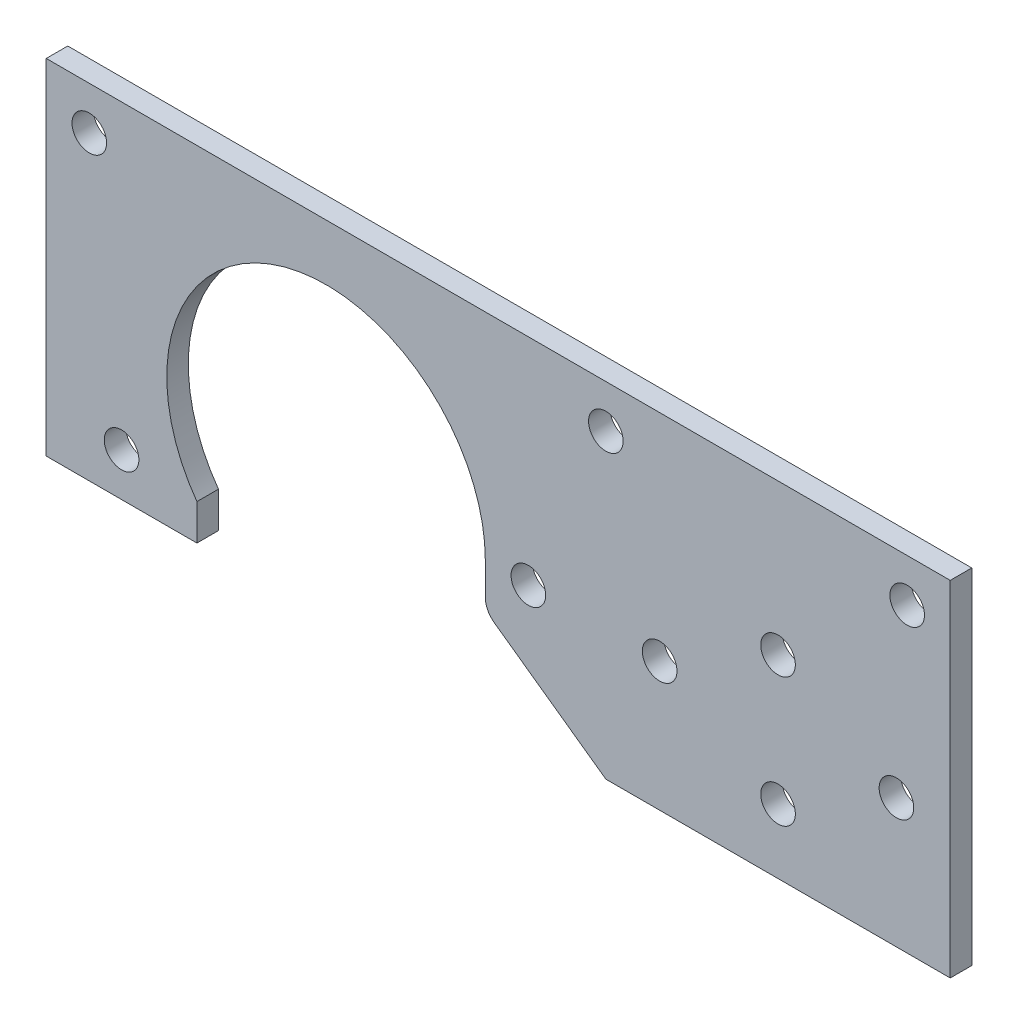
SolidWorks part; units mm, degrees
ref_plane "Front Plane" through (0, 0, 0) normal (0, 0, 1) x (1, 0, 0)
ref_plane "Top Plane" through (0, 0, 0) normal (0, 1, 0) x (1, 0, 0)
ref_plane "Right Plane" through (0, 0, 0) normal (1, 0, 0) x (0, 0, -1)
sketch "Sketch1" plane through (0, 0, 0) normal (0, 0, 1) x (1, 0, 0)
  line L0 (0, 0) -> (0, 50.8)
  line L1 (0, 50.8) -> (-133.35, 50.8)
  line L2 (-133.35, 50.8) -> (-133.35, 0)
  line L3 (-133.35, 0) -> (-111.125, 0)
  line L4 (-111.125, 0) -> (-111.125, 5.2982)
  line L8 (-50.8, 0) -> (0, 0)
  line L9 (-25.4, 28.575) -> (-25.4, 9.525) construction
  line L13 (-68.58, 12.7) -> (-50.8, 0)
  line L14 (-68.58, 19.05) -> (-68.58, 12.7)
  arc A0 (-111.125, 5.2982) -> (-68.58, 19.05) centre (-92.075, 19.05) cw
  circle A1 centre (-25.4, 9.525) radius 2.5527
  circle A2 centre (-25.4, 28.575) radius 2.5527
  circle A3 centre (-7.9375, 19.05) radius 2.5527
  circle A4 centre (-42.8625, 19.05) radius 2.5527
  point P0 (0, 0)
  dimension "D2" = 46.99
  dimension "D10" = 5.1054
  dimension "D7" = 12.7
  dimension "D11" = 25.4
  dimension "D3" = 34.925
  dimension "D4" = 92.075
  dimension "D5" = 19.05
  dimension "D6" = 9.525
  dimension "D8" = 9.525
  dimension "D9" = 22.225
  dimension "D12" = 31.75
  dimension "D13" = 50.8
  dimension "D14" = 133.35
  dimension "D21" = 50.8
extrude "Boss-Extrude1" add sketch "Sketch1" along normal blind 3.175
sketch "Sketch2" plane through (0, 0, 3.175) normal (0, 0, 1) x (1, 0, 0)
  line L1 (0, 0) -> (0, 50.8) construction
  line L2 (-50.8, 0) -> (0, 0) construction
  circle A0 centre (0, -6.35) radius 15.875
  circle A1 centre (-50.8, -6.35) radius 15.875
  dimension "D1" = 31.75
  dimension "D2" = 6.35
  dimension "D3" = 50.8
extrude "Cut-Extrude1" [suppressed] cut sketch "Sketch2" against normal through all
sketch "Sketch3" plane through (0, 0, 0) normal (0, 0, -1) x (-1, 0, 0)
  line L0 (0, 50.8) -> (133.35, 50.8) construction
  line L1 (0, 0) -> (0, 50.8) construction
  line L2 (133.35, 0) -> (111.125, 0) construction
  line L3 (50.8, 0) -> (0, 0) construction
  line L4 (68.58, 19.05) -> (68.58, 12.7) construction
  circle A0 centre (122.2375, 6.35) radius 2.5527
  circle A1 centre (127, 44.45) radius 2.5527
  circle A2 centre (6.35, 44.45) radius 2.5527
  circle A3 centre (50.8, 44.45) radius 2.5527
  circle A4 centre (62.23, 19.05) radius 2.5527
  circle A5 centre (25.4, 28.575) radius 2.5527 construction
  point P19 (122.2375, 0)
other "AlignGroup1" parameters "D1"=133.35, "D2"=133.35, "D3"=50.8, "D4"=127, "D5"=5.0582, "D6"=16.1816, "D7"=6.5416
sketch "Sketch4" plane through (0, 0, 3.175) normal (0, 0, 1) x (1, 0, 0)
  line L1 (-133.35, 0) -> (0, 0)
  line L2 (-133.35, 0) -> (-133.35, 50.8)
  line L3 (-133.35, 50.8) -> (0, 50.8)
  line L4 (0, 0) -> (0, 50.8)
  dimension "D1" = 133.35
  dimension "D2" = 50.8
extrude "Cut-Extrude2" cut sketch "Sketch3" against normal through all
fillet "Fillet1" radius 3.175 1 edges at (-68.58, 12.7, 1.5875)
